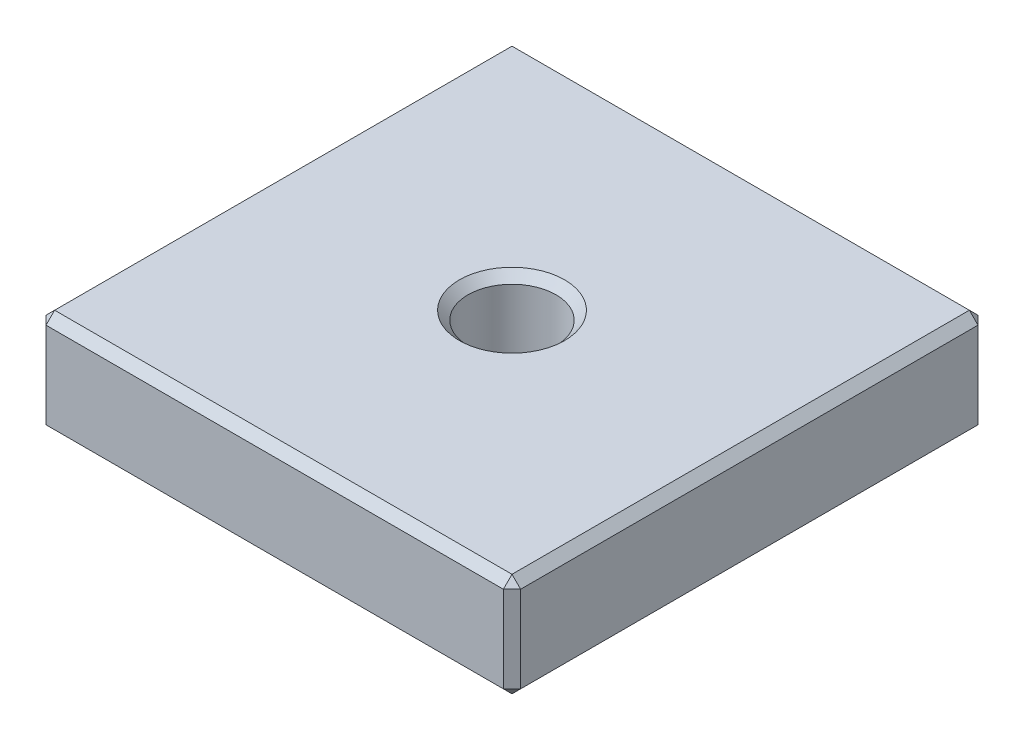
SolidWorks part; units mm, degrees
ref_plane "Plan de face" through (0, 0, 0) normal (0, 0, 1) x (1, 0, 0)
ref_plane "Plan de dessus" through (0, 0, 0) normal (0, 1, 0) x (1, 0, 0)
ref_plane "Plan de droite" through (0, 0, 0) normal (1, 0, 0) x (0, 0, -1)
sketch "Esquisse1" plane through (0, 0, 0) normal (0, 1, 0) x (1, 0, 0)
  line L0 (0, 27.5) -> (55, 27.5) construction
  line L1 (0, 0) -> (55, 0)
  line L2 (0, 0) -> (0, 55)
  line L3 (0, 55) -> (55, 55)
  line L4 (55, 0) -> (55, 55)
  line L5 (27.5, 55) -> (27.5, 0) construction
extrude "Boss.-Extru.1" add sketch "Esquisse1" along normal blind 12
hole_wizard "Trou taraudé M121" positions "Esquisse3" profile "Esquisse2" tap size "M12" standard "ISO" end condition through all
sketch "Esquisse3" plane through (0, 0, 0) normal (0, -1, 0) x (1, 0, 0)
  point P0 (27.5, -27.5)
sketch "Esquisse2" plane through (27.5, 0, -27.5) normal (1, 0, 0) x (0, 0, -1)
  line L0 (0, 0) -> (0, 12)
  line L1 (0, 12) -> (5.1, 12)
  line L2 (5.1, 12) -> (5.1, 0)
  line L5 (5.1, 0) -> (0, 0)
  line L11 (0, -6.35) -> (0, 107.95) construction
  dimension "Diamètre du trou pour taraudage jusqu'au prochain" = 10.2
  dimension "Profondeur du trou pour taraudage jusqu'au prochain" = 12
cosmetic thread "Filetage de perçage1" parameters "D2"=12
sketch "Esquisse4" plane through (0, 0, 0) normal (0, -1, 0) x (1, 0, 0)
  line L0 (27.5, -55) -> (27.5, 0) construction
  line L1 (55, -55) -> (0, -55) construction
  line L2 (0, 0) -> (55, 0) construction
  line L3 (0, -27.5) -> (55, -27.5) construction
  line L4 (0, -55) -> (0, 0) construction
  line L5 (55, 0) -> (55, -55) construction
  point P12 (27.5, -27.5)
chamfer "Chanfrein1" distance 1 angle 45 14 edges at (27.5, 12, -32.6) (27.5, 0, -32.6) (27.5, 12, -55) (55, 12, -27.5) (27.5, 12, 0) (0, 12, -27.5) (27.5, 0, 0) (55, 6, 0) (55, 0, -27.5) (55, 6, -55) (27.5, 0, -55) (0, 6, 0) (0, 0, -27.5) (0, 6, -55)
